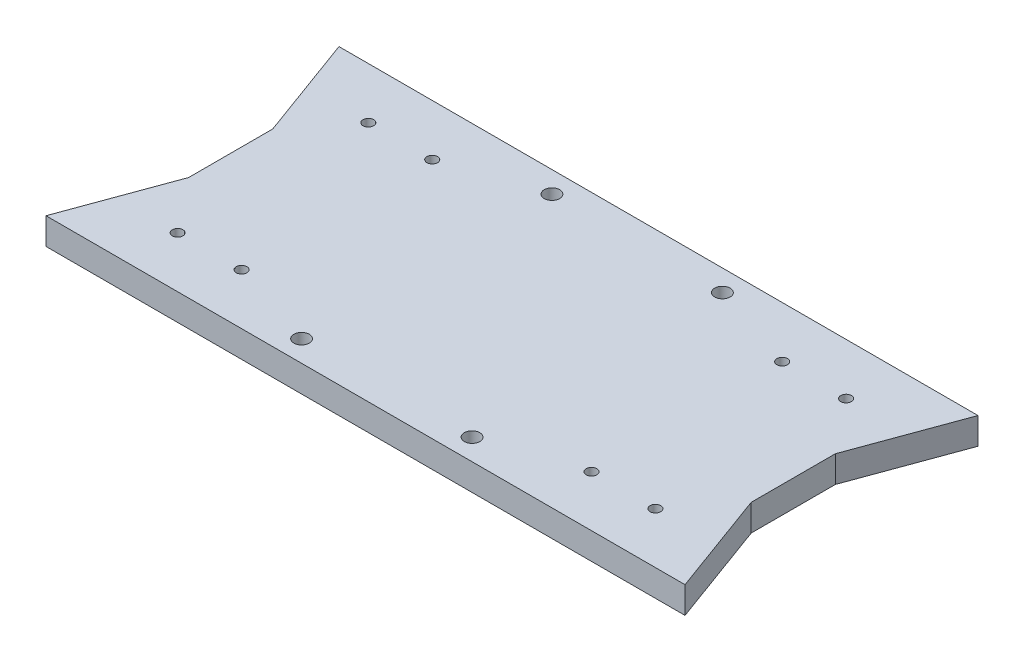
SolidWorks part; units mm, degrees
material "ABS PC"
ref_plane "Front Plane" through (0, 0, 0) normal (0, 0, 1) x (1, 0, 0)
ref_plane "Top Plane" through (0, 0, 0) normal (0, 1, 0) x (1, 0, 0)
ref_plane "Right Plane" through (0, 0, 0) normal (1, 0, 0) x (0, 0, -1)
sketch "Sketch1" plane through (0, 0, 0) normal (0, 1, 0) x (1, 0, 0)
  line L0 (28.7276, 102.6327) -> (-38.3337, 102.6327) construction
  line L1 (-38.3337, 32.7827) -> (28.7276, 32.7827)
  line L2 (-38.3337, 32.7827) -> (-38.3337, 102.6327)
  line L3 (-38.3337, 102.6327) -> (28.7276, 102.6327)
  line L4 (28.7276, 32.7827) -> (28.7276, 102.6327)
  line L5 (-38.3337, 32.7827) -> (28.7276, 32.7827) construction
  line L6 (-38.3337, 102.6327) -> (-38.3337, 32.7827) construction
  circle A1 centre (3.3813, 90.4077) radius 1.27
  circle A2 centre (18.6213, 90.4077) radius 1.27
  circle A3 centre (3.3813, 44.9477) radius 1.27
  circle A4 centre (18.6213, 44.9477) radius 1.27
  dimension "D5" = 2.54
  dimension "D6" = 2.54
  dimension "D7" = 2.54
  dimension "D8" = 2.54
  dimension "D1" = 0
  dimension "D2" = 0
  dimension "D3" = 0
  dimension "D4" = 0
extrude "Boss-Extrude1" add sketch "Sketch1" along normal blind 6.35
sketch "Sketch2" plane through (0, 6.35, 0) normal (0, 1, 0) x (1, 0, 0)
  line L1 (28.7276, 57.6777) -> (7.7513, 57.6777)
  line L2 (28.7276, 57.6777) -> (28.7276, 77.7377)
  line L3 (28.7276, 77.7377) -> (7.7513, 77.7377)
  line L4 (7.7513, 57.6777) -> (7.7513, 77.7377)
extrude "Boss-Extrude2" add sketch "Sketch2" along normal blind 12.7
sketch "Sketch3" plane through (0, 6.35, 0) normal (0, 1, 0) x (1, 0, 0)
  line L1 (37.8413, 102.6327) -> (28.7276, 77.7377)
  line L2 (28.7276, 77.7377) -> (28.7276, 102.6327)
  line L3 (28.7276, 102.6327) -> (37.8413, 102.6327)
  line L4 (28.7276, 57.6777) -> (37.8413, 32.7827)
  line L5 (37.8413, 32.7827) -> (28.7276, 32.7827)
  line L6 (28.7276, 32.7827) -> (28.7276, 57.6777)
extrude "Boss-Extrude3" add sketch "Sketch3" against normal blind 6.35
mirror "Mirror2" about plane through (-38.3337, 6.35, -32.7827) normal (1, 0, 0) of "Boss-Extrude1", "Boss-Extrude2", "Boss-Extrude3"
sketch "Sketch4" plane through (0, 0, -32.7827) normal (0, 0, 1) x (1, 0, 0)
  line L1 (37.8413, 6.35) -> (-133.1569, 6.35)
  line L2 (37.8413, 6.35) -> (37.8413, 24.3471)
  line L3 (37.8413, 24.3471) -> (-133.1569, 24.3471)
  line L4 (-133.1569, 6.35) -> (-133.1569, 24.3471)
extrude "Cut-Extrude1" cut sketch "Sketch4" against normal through all
sketch "Sketch5" plane through (0, 0, 0) normal (0, -1, 0) x (1, 0, 0)
  circle A1 centre (21.0248, -94.445) radius 0.1639
sketch "Sketch6" plane through (0, 0, 0) normal (0, -1, 0) x (-1, 0, 0)
  circle A0 centre (-37.8413, 34.6877) radius 31.75
  dimension "D1" = 63.5
sketch "Sketch7" plane through (0, 6.35, 0) normal (0, 1, 0) x (1, 0, 0)
  circle A0 centre (3.3813, 90.4077) radius 1.2687
  circle A1 centre (18.6213, 90.4077) radius 1.2687
  circle A2 centre (3.3813, 44.9477) radius 1.2687
  circle A4 centre (18.6213, 44.9477) radius 1.2687
  dimension "D1" = 2.5375
  dimension "D2" = 2.5375
  dimension "D3" = 2.5375
  dimension "D4" = 2.5375
sketch "Sketch8" plane through (0, 6.35, 0) normal (0, 1, 0) x (1, 0, 0)
  line L0 (37.8413, 102.6327) -> (-114.5087, 102.6327) construction
  line L1 (-23.0937, 188.9927) -> (-23.0937, 92.4727) construction
  line L2 (-53.5737, 188.9927) -> (-53.5737, 92.4727) construction
  line L3 (-114.5087, 32.7827) -> (37.8413, 32.7827) construction
  circle A0 centre (-58.6537, 97.5527) radius 1.8415
  circle A1 centre (-18.0137, 97.5527) radius 1.8415
  circle A2 centre (-18.0137, 37.8627) radius 1.8415
  circle A3 centre (-58.6537, 37.8627) radius 1.8415
  dimension "D1" = 3.683
  dimension "D2" = 3.683
  dimension "D3" = 3.683
  dimension "D4" = 3.683
  dimension "D5" = 5.08
  dimension "D6" = 5.08
  dimension "D7" = 5.08
  dimension "D8" = 5.08
  dimension "D9" = 5.08
  dimension "D10" = 5.08
extrude "Cut-Extrude3" cut sketch "Sketch8" against normal blind 13.716
